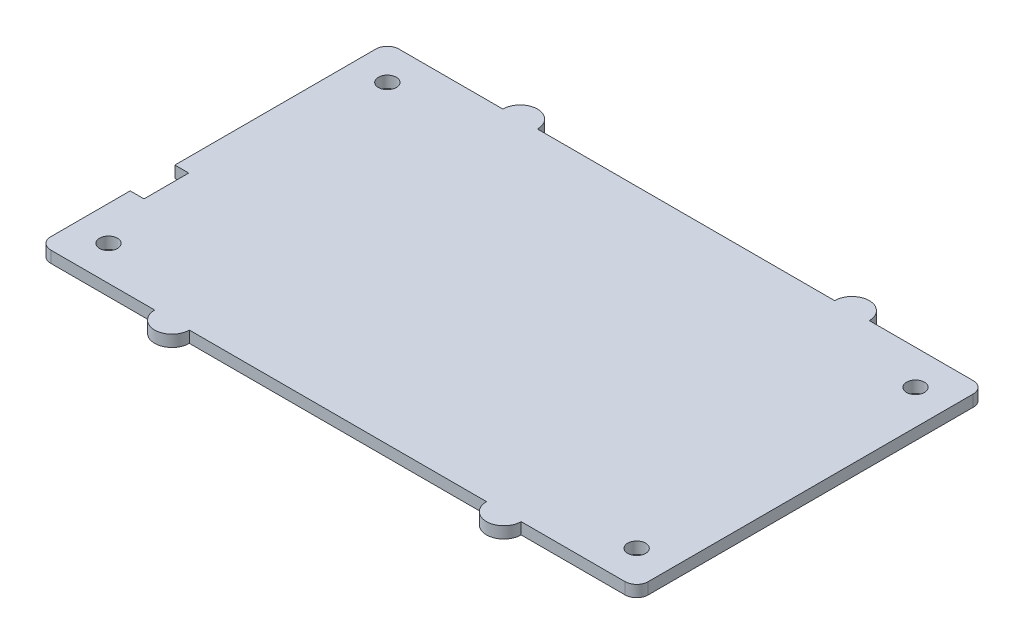
SolidWorks part; units mm, degrees
ref_plane "前视基准面" through (0, 0, 0) normal (0, 0, 1) x (1, 0, 0)
ref_plane "上视基准面" through (0, 0, 0) normal (0, 1, 0) x (1, 0, 0)
ref_plane "右视基准面" through (0, 0, 0) normal (1, 0, 0) x (0, 0, -1)
sketch "草图1" plane through (0, 0, 0) normal (0, 1, 0) x (1, 0, 0)
  line L0 (0, 0) -> (-12.7865, 0) construction
  line L1 (0, 0) -> (0, 22.3168) construction
  line L2 (91.46, 0) -> (91.46, 15.7584) construction
  line L3 (91.46, 48.29) -> (79.4981, 48.29) construction
  line L4 (-6, 0) -> (-6, 22.3168) construction
  line L5 (0, -6) -> (-12.7865, -6) construction
  line L6 (91.46, 54.29) -> (79.4981, 54.29) construction
  line L7 (97.46, 0) -> (97.46, 15.7584) construction
  line L8 (95.46, 54.29) -> (-4, 54.29)
  line L9 (-6, 52.29) -> (-6, -4)
  line L10 (-4, -6) -> (95.46, -6)
  line L11 (97.46, -4) -> (97.46, 52.29)
  line L12 (0, -9) -> (-12.7865, -9) construction
  line L13 (14, 0) -> (14, 22.3168) construction
  line L14 (34, 0) -> (34, 22.3168) construction
  line L15 (77.46, 0) -> (77.46, 15.7584) construction
  line L16 (57.46, 0) -> (57.46, 15.7584) construction
  line L17 (91.46, 57.29) -> (79.4981, 57.29) construction
  line L18 (0, 9.75) -> (-12.7865, 9.75) construction
  line L19 (0, 17.45) -> (-12.7865, 17.45) construction
  line L20 (-3.6, 52.29) -> (-3.6, -4) construction
  line L22 (-6, 17.4939) -> (-3.6, 17.4939)
  line L23 (-6, 17.4939) -> (-6, 9.75)
  line L24 (-6, 9.75) -> (-3.6, 9.75)
  line L25 (-3.6, 17.4939) -> (-3.6, 9.75)
  circle A0 centre (0, 0) radius 1.55
  circle A1 centre (91.46, 0) radius 1.55
  circle A2 centre (91.46, 48.29) radius 1.55
  circle A3 centre (0, 48.29) radius 1.55
  circle A4 centre (-4, 52.29) radius 2
  circle A5 centre (-4, -4) radius 2
  circle A6 centre (95.46, -4) radius 2
  circle A7 centre (95.46, 52.29) radius 2
  circle A8 centre (17, 54.29) radius 3
  circle A11 centre (74.46, 54.29) radius 3
  circle A12 centre (17, -6) radius 3
  circle A15 centre (74.46, -6) radius 3
  dimension "D1" = 2
  dimension "D9" = 20
  dimension "D7" = 3
  dimension "D13" = 15.75
  dimension "D8" = 20
  dimension "D3" = 6
  dimension "D4" = 6
  dimension "D5" = 6
  dimension "D6" = 6
  dimension "D10" = 20
  dimension "D11" = 20
  dimension "D12" = 3
  dimension "D14" = 7.7
  dimension "D15" = 2.4
  dimension "D2" = 2
extrude "凸台-拉伸1" add sketch "草图1" along normal blind 2 contours A7 L8 A4 L9 A5 L10 A6 L11 A3 A2 A1 A0 | A5 | A4 | A7 | A6
